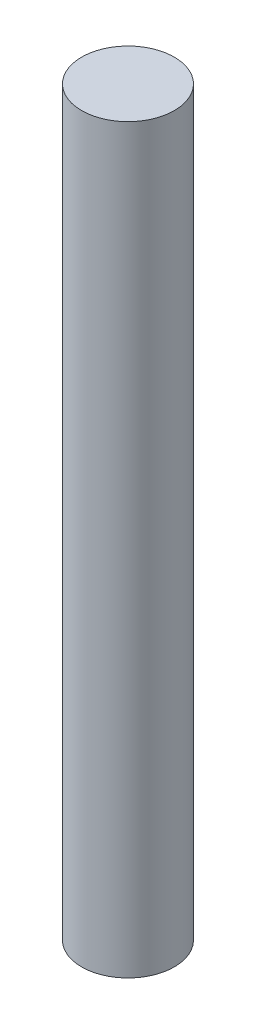
SolidWorks part; units mm, degrees
ref_plane "Front Plane" through (0, 0, 0) normal (0, 0, 1) x (1, 0, 0)
ref_plane "Top Plane" through (0, 0, 0) normal (0, 1, 0) x (1, 0, 0)
ref_plane "Right Plane" through (0, 0, 0) normal (1, 0, 0) x (0, 0, -1)
sketch "Sketch1" plane through (0, 0, 0) normal (0, 1, 0) x (1, 0, 0)
  circle A0 centre (0, 0) radius 12.5
  dimension "D1" = 25
extrude "Boss-Extrude1" add sketch "Sketch1" along normal blind 200
